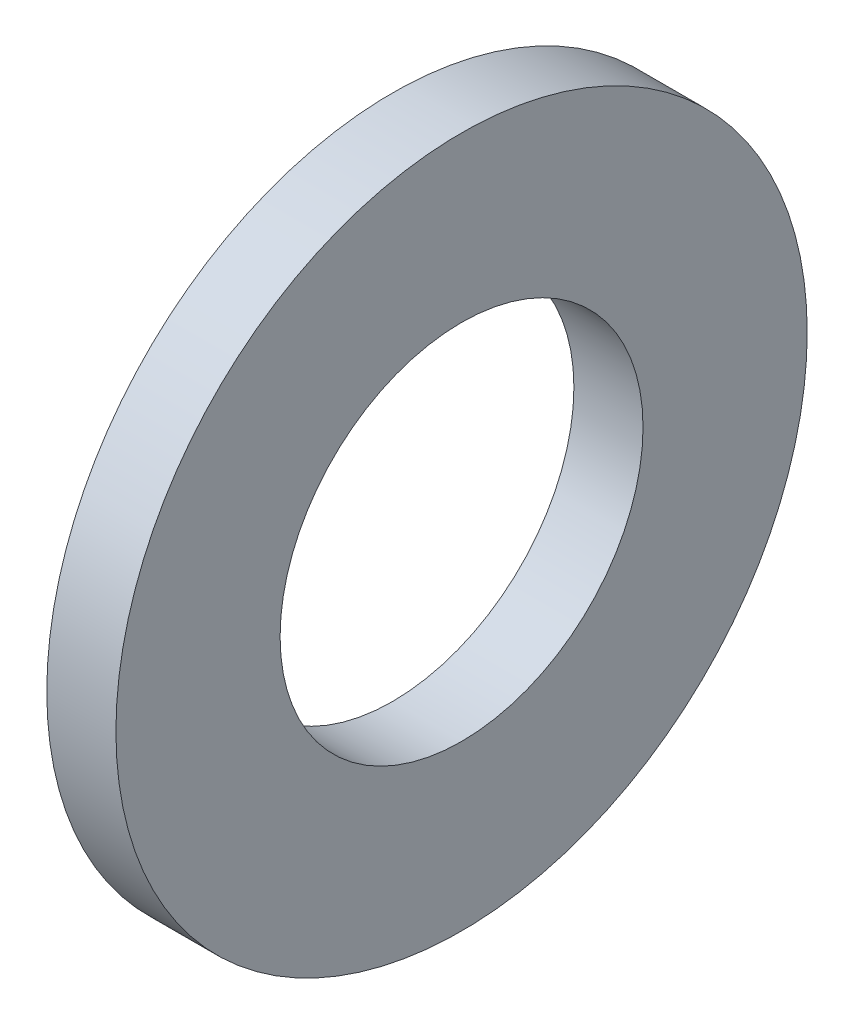
SolidWorks part; units mm, degrees
ref_plane "Plane1" through (0, 0, 0) normal (0, 0, 1) x (1, 0, 0)
ref_plane "Plane2" through (0, 0, 0) normal (0, 1, 0) x (1, 0, 0)
ref_plane "Plane3" through (0, 0, 0) normal (1, 0, 0) x (0, 0, -1)
sketch "Sketch1" plane through (0, 0, 0) normal (0, 0, 1) x (1, 0, 0)
  line L0 (-34.925, 0) -> (9.525, 0) construction
  line L1 (0, 4.2) -> (0, 8)
  line L2 (0, 8) -> (-1.6, 8)
  line L3 (-1.6, 8) -> (-1.6, 4.2)
  line L4 (-1.6, 4.2) -> (0, 4.2)
revolve "Base-Revolve" add sketch "Sketch1" angle 360 about L0
chamfer "ODChamfer" [suppressed] distance 0.2 angle 45
equation "\"D1@ODChamfer\" =  \"Thickness@Sketch1\" * 0.25"
